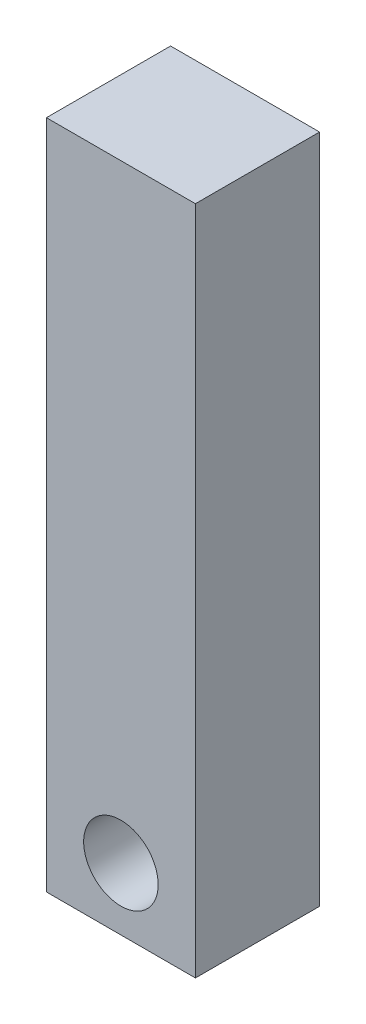
SolidWorks part; units mm, degrees
ref_plane "Face" through (0, 0, 0) normal (0, 0, 1) x (1, 0, 0)
ref_plane "Dessus" through (0, 0, 0) normal (0, 1, 0) x (1, 0, 0)
ref_plane "Droite" through (0, 0, 0) normal (1, 0, 0) x (0, 0, -1)
sketch "Esquisse1" plane through (0, 0, 0) normal (0, 0, 1) x (1, 0, 0)
  line L5 (-12, -54.01) -> (0, -54.01)
  line L6 (-12, -54.01) -> (-12, 0)
  line L7 (-12, 0) -> (0, 0)
  line L8 (0, -54.01) -> (0, 0)
  dimension "D1" = 54.01
  dimension "D2" = 12
extrude "Boss.-Extru.1" add sketch "Esquisse1" along normal blind 10
sketch "Esquisse2" plane through (0, 0, 10) normal (0, 0, 1) x (1, 0, 0)
  circle A0 centre (-6, -49) radius 3
extrude "Enlèv. mat.-Extru.1" cut sketch "Esquisse2" against normal blind 10
